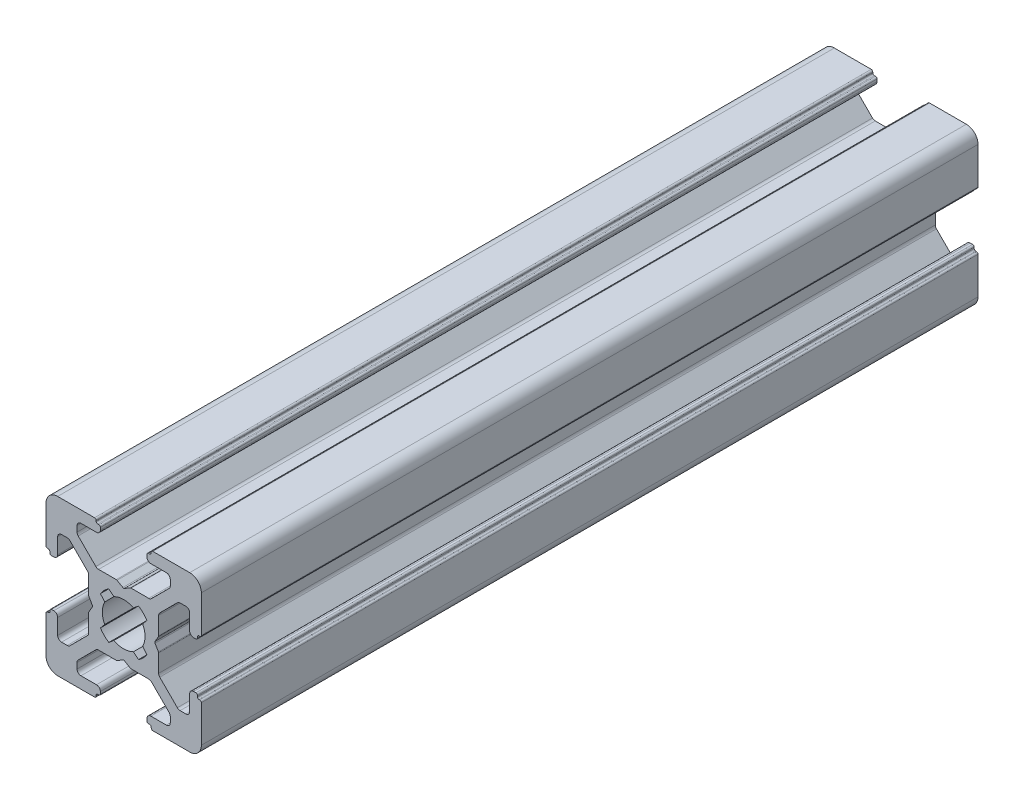
SolidWorks part; units mm, degrees
material "6063-T6"
ref_plane "Front Plane" through (0, 0, 0) normal (0, 0, 1) x (1, 0, 0)
ref_plane "Top Plane" through (0, 0, 0) normal (0, 1, 0) x (1, 0, 0)
ref_plane "Right Plane" through (0, 0, 0) normal (1, 0, 0) x (0, 0, -1)
sketch "Sketch1" plane through (0, 0, 0) normal (0, 0, 1) x (1, 0, 0)
  line L0 (0, 13.3675) -> (0, -10.9159) construction
  line L1 (-12.9725, 0) -> (15.1887, 0) construction
  line L2 (-3.5, 8.5) -> (-5.5, 8.5)
  line L3 (-3.55, 9.7) -> (-3.55, 9.8)
  line L4 (-6, 7.2678) -> (-6, 8)
  line L5 (-7.2678, 6) -> (-8, 6)
  line L6 (-3.75, 10) -> (-8.5, 10)
  line L7 (-9.7, 3.55) -> (-9.8, 3.55)
  line L8 (-9.5, 3.2) -> (-9.5, 3.35)
  line L9 (-9, 3) -> (-9.3, 3)
  line L10 (-4.4732, 0.8536) -> (-4.0381, 0.1)
  line L11 (-4.5, 3.2322) -> (-4.5, 0.9536)
  line L12 (-8.5, 3.5) -> (-8.5, 5.5)
  line L13 (-10, 3.75) -> (-10, 8.5)
  line L14 (-3.5858, 4.6464) -> (-5.8536, 6.9142)
  line L15 (-4.6464, 3.5858) -> (-6.9142, 5.8536)
  line L16 (-3.2, 9.5) -> (-3.35, 9.5)
  line L17 (-3, 9) -> (-3, 9.3)
  line L18 (-0.8536, 4.4732) -> (-0.1, 4.0381)
  line L19 (-3.2322, 4.5) -> (-0.9536, 4.5)
  line L20 (-1.2582, 2.4453) -> (-1.9139, 2.9896)
  line L21 (-2.4453, 1.2582) -> (-2.9922, 1.9099)
  line L22 (3.5, -8.5) -> (5.5, -8.5)
  line L23 (3.55, -9.7) -> (3.55, -9.8)
  line L24 (6, -7.2678) -> (6, -8)
  line L25 (7.2678, -6) -> (8, -6)
  line L26 (3.75, -10) -> (8.5, -10)
  line L27 (9.7, -3.55) -> (9.8, -3.55)
  line L28 (9.5, -3.2) -> (9.5, -3.35)
  line L29 (9, -3) -> (9.3, -3)
  line L30 (4.4732, -0.8536) -> (4.0381, -0.1)
  line L31 (4.5, -3.2322) -> (4.5, -0.9536)
  line L32 (8.5, -3.5) -> (8.5, -5.5)
  line L33 (10, -3.75) -> (10, -8.5)
  line L34 (3.5858, -4.6464) -> (5.8536, -6.9142)
  line L35 (4.6464, -3.5858) -> (6.9142, -5.8536)
  line L36 (3.2, -9.5) -> (3.35, -9.5)
  line L37 (3, -9) -> (3, -9.3)
  line L38 (0.8536, -4.4732) -> (0.1, -4.0381)
  line L39 (3.2322, -4.5) -> (0.9536, -4.5)
  line L40 (1.2582, -2.4453) -> (1.9139, -2.9896)
  line L41 (2.4453, -1.2582) -> (2.9922, -1.9099)
  line L42 (-2.4453, -1.2582) -> (-2.9922, -1.9099)
  line L43 (-1.2582, -2.4453) -> (-1.9139, -2.9896)
  line L44 (-3.2322, -4.5) -> (-0.9536, -4.5)
  line L45 (-0.8536, -4.4732) -> (-0.1, -4.0381)
  line L46 (-3, -9) -> (-3, -9.3)
  line L47 (-3.2, -9.5) -> (-3.35, -9.5)
  line L48 (-4.6464, -3.5858) -> (-6.9142, -5.8536)
  line L49 (-3.5858, -4.6464) -> (-5.8536, -6.9142)
  line L50 (-10, -3.75) -> (-10, -8.5)
  line L51 (-8.5, -3.5) -> (-8.5, -5.5)
  line L52 (-4.5, -3.2322) -> (-4.5, -0.9536)
  line L53 (-4.4732, -0.8536) -> (-4.0381, -0.1)
  line L54 (-9, -3) -> (-9.3, -3)
  line L55 (-9.5, -3.2) -> (-9.5, -3.35)
  line L56 (-9.7, -3.55) -> (-9.8, -3.55)
  line L57 (2.4453, 1.2582) -> (2.9922, 1.9099)
  line L58 (1.2582, 2.4453) -> (1.9139, 2.9896)
  line L59 (3.2322, 4.5) -> (0.9536, 4.5)
  line L60 (0.8536, 4.4732) -> (0.1, 4.0381)
  line L61 (-3.75, -10) -> (-8.5, -10)
  line L62 (-7.2678, -6) -> (-8, -6)
  line L63 (-6, -7.2678) -> (-6, -8)
  line L64 (3, 9) -> (3, 9.3)
  line L65 (3.2, 9.5) -> (3.35, 9.5)
  line L66 (4.6464, 3.5858) -> (6.9142, 5.8536)
  line L67 (3.5858, 4.6464) -> (5.8536, 6.9142)
  line L68 (10, 3.75) -> (10, 8.5)
  line L69 (8.5, 3.5) -> (8.5, 5.5)
  line L70 (4.5, 3.2322) -> (4.5, 0.9536)
  line L71 (4.4732, 0.8536) -> (4.0381, 0.1)
  line L72 (9, 3) -> (9.3, 3)
  line L73 (9.5, 3.2) -> (9.5, 3.35)
  line L74 (9.7, 3.55) -> (9.8, 3.55)
  line L75 (3.75, 10) -> (8.5, 10)
  line L76 (7.2678, 6) -> (8, 6)
  line L77 (6, 7.2678) -> (6, 8)
  line L78 (3.55, 9.7) -> (3.55, 9.8)
  line L79 (3.5, 8.5) -> (5.5, 8.5)
  line L80 (-3.55, -9.7) -> (-3.55, -9.8)
  line L81 (-3.5, -8.5) -> (-5.5, -8.5)
  arc A0 (-10, 8.5) -> (-8.5, 10) centre (-8.5, 8.5) cw
  arc A1 (-8.5, 5.5) -> (-8, 6) centre (-8, 5.5) cw
  arc A2 (-7.2678, 6) -> (-6.9142, 5.8536) centre (-7.2678, 5.5) cw
  arc A3 (-5.8536, 6.9142) -> (-6, 7.2678) centre (-5.5, 7.2678) cw
  arc A4 (-6, 8) -> (-5.5, 8.5) centre (-5.5, 8) cw
  arc A5 (-9.7, 3.55) -> (-9.5, 3.35) centre (-9.7, 3.35) cw
  arc A6 (-9.8, 3.55) -> (-10, 3.75) centre (-9.8, 3.75) cw
  arc A7 (-9.3, 3) -> (-9.5, 3.2) centre (-9.3, 3.2) cw
  arc A8 (-8.5, 3.5) -> (-9, 3) centre (-9, 3.5) cw
  arc A9 (-4.6464, 3.5858) -> (-4.5, 3.2322) centre (-5, 3.2322) cw
  arc A10 (-4.4732, 0.8536) -> (-4.5, 0.9536) centre (-4.3, 0.9536) cw
  arc A11 (-4.0381, 0.1) -> (-4.0381, -0.1) centre (-4.2113, 0) cw
  arc A12 (-3.2, 9.5) -> (-3, 9.3) centre (-3.2, 9.3) cw
  arc A13 (-0.9536, 4.5) -> (-0.8536, 4.4732) centre (-0.9536, 4.3) cw
  arc A14 (-2.9922, 1.9099) -> (-1.9139, 2.9896) centre (0, 0) cw
  arc A15 (-3.2322, 4.5) -> (-3.5858, 4.6464) centre (-3.2322, 5) cw
  arc A16 (-3.75, 10) -> (-3.55, 9.8) centre (-3.75, 9.8) cw
  arc A17 (-3.35, 9.5) -> (-3.55, 9.7) centre (-3.35, 9.7) cw
  arc A18 (2.4453, -1.2582) -> (2.4453, 1.2582) centre (0, 0) ccw
  arc A19 (-3, 9) -> (-3.5, 8.5) centre (-3.5, 9) cw
  arc A20 (-2.4453, -1.2582) -> (-2.4453, 1.2582) centre (0, 0) cw
  arc A21 (10, -8.5) -> (8.5, -10) centre (8.5, -8.5) cw
  arc A22 (8.5, -5.5) -> (8, -6) centre (8, -5.5) cw
  arc A23 (7.2678, -6) -> (6.9142, -5.8536) centre (7.2678, -5.5) cw
  arc A24 (5.8536, -6.9142) -> (6, -7.2678) centre (5.5, -7.2678) cw
  arc A25 (6, -8) -> (5.5, -8.5) centre (5.5, -8) cw
  arc A26 (9.7, -3.55) -> (9.5, -3.35) centre (9.7, -3.35) cw
  arc A27 (9.8, -3.55) -> (10, -3.75) centre (9.8, -3.75) cw
  arc A28 (9.3, -3) -> (9.5, -3.2) centre (9.3, -3.2) cw
  arc A29 (8.5, -3.5) -> (9, -3) centre (9, -3.5) cw
  arc A30 (4.6464, -3.5858) -> (4.5, -3.2322) centre (5, -3.2322) cw
  arc A31 (4.4732, -0.8536) -> (4.5, -0.9536) centre (4.3, -0.9536) cw
  arc A32 (3.2, -9.5) -> (3, -9.3) centre (3.2, -9.3) cw
  arc A33 (-0.1, -4.0381) -> (0.1, -4.0381) centre (0, -4.2113) cw
  arc A34 (0.9536, -4.5) -> (0.8536, -4.4732) centre (0.9536, -4.3) cw
  arc A35 (2.9922, -1.9099) -> (1.9139, -2.9896) centre (0, 0) cw
  arc A36 (1.2582, -2.4453) -> (-1.2582, -2.4453) centre (0, 0) cw
  arc A37 (3.2322, -4.5) -> (3.5858, -4.6464) centre (3.2322, -5) cw
  arc A38 (3.75, -10) -> (3.55, -9.8) centre (3.75, -9.8) cw
  arc A39 (3.35, -9.5) -> (3.55, -9.7) centre (3.35, -9.7) cw
  arc A40 (3, -9) -> (3.5, -8.5) centre (3.5, -9) cw
  arc A41 (-3, -9) -> (-3.5, -8.5) centre (-3.5, -9) ccw
  arc A42 (-3.35, -9.5) -> (-3.55, -9.7) centre (-3.35, -9.7) ccw
  arc A43 (-3.75, -10) -> (-3.55, -9.8) centre (-3.75, -9.8) ccw
  arc A44 (-3.2322, -4.5) -> (-3.5858, -4.6464) centre (-3.2322, -5) ccw
  arc A45 (-2.9922, -1.9099) -> (-1.9139, -2.9896) centre (0, 0) ccw
  arc A46 (-0.9536, -4.5) -> (-0.8536, -4.4732) centre (-0.9536, -4.3) ccw
  arc A47 (-3.2, -9.5) -> (-3, -9.3) centre (-3.2, -9.3) ccw
  arc A48 (-4.4732, -0.8536) -> (-4.5, -0.9536) centre (-4.3, -0.9536) ccw
  arc A49 (3, 9) -> (3.5, 8.5) centre (3.5, 9) ccw
  arc A50 (3.35, 9.5) -> (3.55, 9.7) centre (3.35, 9.7) ccw
  arc A51 (3.75, 10) -> (3.55, 9.8) centre (3.75, 9.8) ccw
  arc A52 (3.2322, 4.5) -> (3.5858, 4.6464) centre (3.2322, 5) ccw
  arc A53 (1.2582, 2.4453) -> (-1.2582, 2.4453) centre (0, 0) ccw
  arc A54 (-4.6464, -3.5858) -> (-4.5, -3.2322) centre (-5, -3.2322) ccw
  arc A55 (-8.5, -3.5) -> (-9, -3) centre (-9, -3.5) ccw
  arc A56 (-9.3, -3) -> (-9.5, -3.2) centre (-9.3, -3.2) ccw
  arc A57 (-9.8, -3.55) -> (-10, -3.75) centre (-9.8, -3.75) ccw
  arc A58 (-9.7, -3.55) -> (-9.5, -3.35) centre (-9.7, -3.35) ccw
  arc A59 (-6, -8) -> (-5.5, -8.5) centre (-5.5, -8) ccw
  arc A60 (2.9922, 1.9099) -> (1.9139, 2.9896) centre (0, 0) ccw
  arc A61 (0.9536, 4.5) -> (0.8536, 4.4732) centre (0.9536, 4.3) ccw
  arc A62 (-0.1, 4.0381) -> (0.1, 4.0381) centre (0, 4.2113) ccw
  arc A63 (-5.8536, -6.9142) -> (-6, -7.2678) centre (-5.5, -7.2678) ccw
  arc A64 (-7.2678, -6) -> (-6.9142, -5.8536) centre (-7.2678, -5.5) ccw
  arc A65 (-8.5, -5.5) -> (-8, -6) centre (-8, -5.5) ccw
  arc A66 (-10, -8.5) -> (-8.5, -10) centre (-8.5, -8.5) ccw
  arc A67 (3.2, 9.5) -> (3, 9.3) centre (3.2, 9.3) ccw
  arc A68 (4.0381, 0.1) -> (4.0381, -0.1) centre (4.2113, 0) ccw
  arc A69 (4.4732, 0.8536) -> (4.5, 0.9536) centre (4.3, 0.9536) ccw
  arc A70 (4.6464, 3.5858) -> (4.5, 3.2322) centre (5, 3.2322) ccw
  arc A71 (8.5, 3.5) -> (9, 3) centre (9, 3.5) ccw
  arc A72 (9.3, 3) -> (9.5, 3.2) centre (9.3, 3.2) ccw
  arc A73 (9.8, 3.55) -> (10, 3.75) centre (9.8, 3.75) ccw
  arc A74 (9.7, 3.55) -> (9.5, 3.35) centre (9.7, 3.35) ccw
  arc A75 (6, 8) -> (5.5, 8.5) centre (5.5, 8) ccw
  arc A76 (5.8536, 6.9142) -> (6, 7.2678) centre (5.5, 7.2678) ccw
  arc A77 (7.2678, 6) -> (6.9142, 5.8536) centre (7.2678, 5.5) ccw
  arc A78 (8.5, 5.5) -> (8, 6) centre (8, 5.5) ccw
  arc A79 (10, 8.5) -> (8.5, 10) centre (8.5, 8.5) ccw
  dimension "D4" = 5.5
  dimension "D1" = 6
  dimension "D2" = 20
  dimension "D3" = 20
  dimension "D5" = 5.5
  dimension "D6" = 10
  dimension "D7" = 6
  dimension "D8" = 6
  dimension "D9" = 6
  dimension "D10" = 5.5
extrude "Extrude1" add sketch "Sketch1" along normal blind 100
sketch "Эскиз1" plane through (-10, 0, 0) normal (-1, 0, 0) x (0, 0, 1)
  line L0 (0, 10) -> (0, -10)
  line L1 (0, -10) -> (20, -10)
  line L2 (100, -10) -> (0, -10) construction
  line L3 (20, -10) -> (0, 10)
  dimension "D1" = 45
